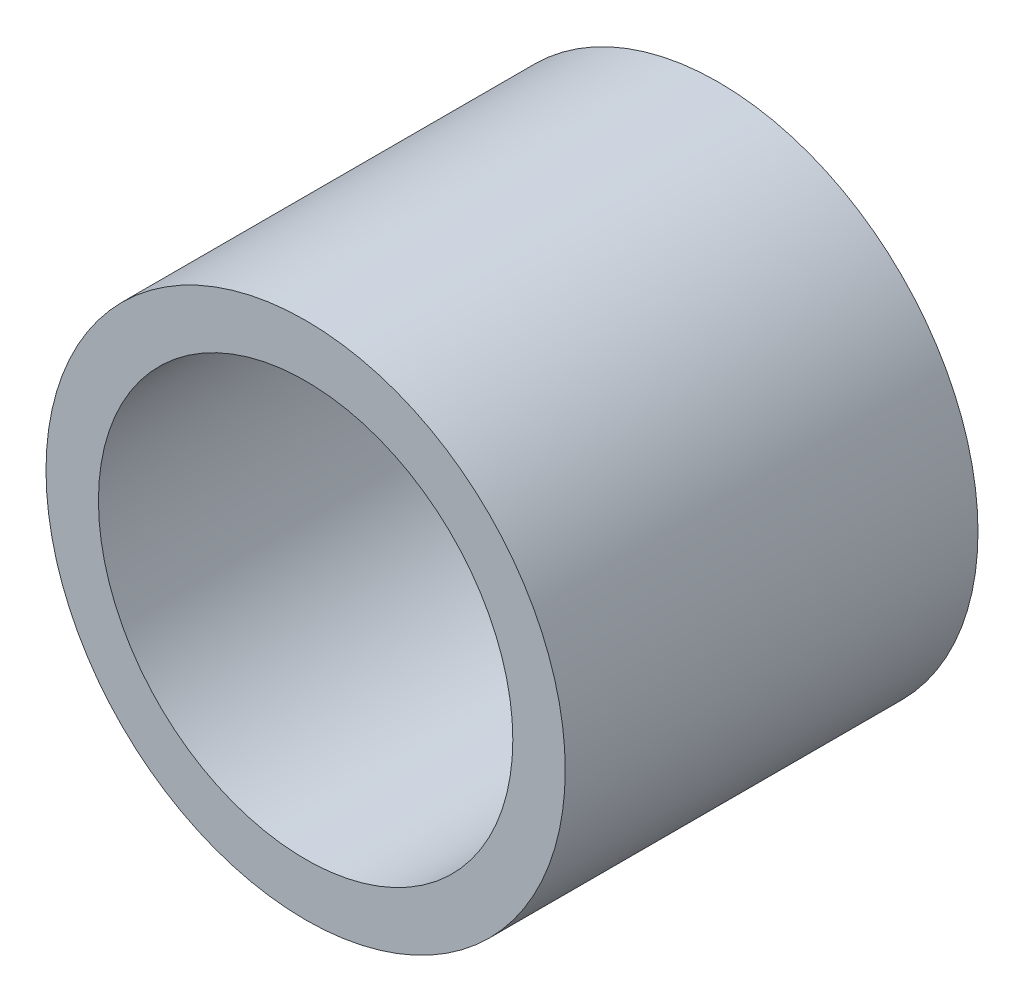
SolidWorks part; units mm, degrees
ref_plane "Front Plane" through (0, 0, 0) normal (0, 0, 1) x (1, 0, 0)
ref_plane "Top Plane" through (0, 0, 0) normal (0, 1, 0) x (1, 0, 0)
ref_plane "Right Plane" through (0, 0, 0) normal (1, 0, 0) x (0, 0, -1)
sketch "Sketch1" plane through (0, 0, 0) normal (0, 0, 1) x (1, 0, 0)
  circle A0 centre (0, 0) radius 3.9942
  circle A1 centre (0, 0) radius 3.1877
  dimension "OD" = 7.9883
  dimension "ID" = 6.3754
sketch "Sketch2" plane through (0, 0, 0) normal (1, 0, 0) x (0, 0, -1)
  line L2 (3.175, 0) -> (-3.175, 0) construction
  line L4 (-3.175, -3.9942) -> (-3.175, 3.9941) construction
  line L5 (-3.175, -3.1877) -> (3.175, -3.1877)
  line L6 (3.175, 3.1877) -> (-3.175, 3.1877)
  line L7 (3.175, -3.9942) -> (3.175, 3.9941) construction
  line L8 (-3.175, 3.9941) -> (3.175, 3.9941) construction
  line L9 (-3.175, -3.9942) -> (3.175, -3.9942) construction
  line L10 (0, 3.9942) -> (0, -3.9942) construction
  line L11 (0, 3.1877) -> (0, -3.1877) construction
  point P4 (0, -3.1877)
  point P7 (0, 3.1877)
  point P8 (0, 0)
  point P12 (-3.175, 0)
  point P15 (3.175, 0)
  point P16 (0, -3.9942)
  point P17 (0, 3.9942)
sketch "Sketch5" plane through (0, 0, 0) normal (0, 0, 1) x (1, 0, 0)
  circle A1 centre (0, 0) radius 3.1877
  circle A2 centre (0, 0) radius 3.1877
  circle A3 centre (0, 0) radius 3.9942
  circle A4 centre (0, 0) radius 3.9942
  dimension "D1" = 0
  dimension "D2" = 0
extrude "Boss-Extrude1" add sketch "Sketch5" along normal mid plane 6.35
sketch "Sketch4" plane through (0, 0, 3.175) normal (0, 0, 1) x (1, 0, 0)
  line L0 (0, 0) -> (-2.254, 2.254)
  line L2 (0, -3.9942) -> (0, 3.9941) construction
  circle A1 centre (0, 0) radius 3.1877 construction
  dimension "D1" = 45
equation "\"D1@Boss-Extrude1\"=\"length@sketch2\""
